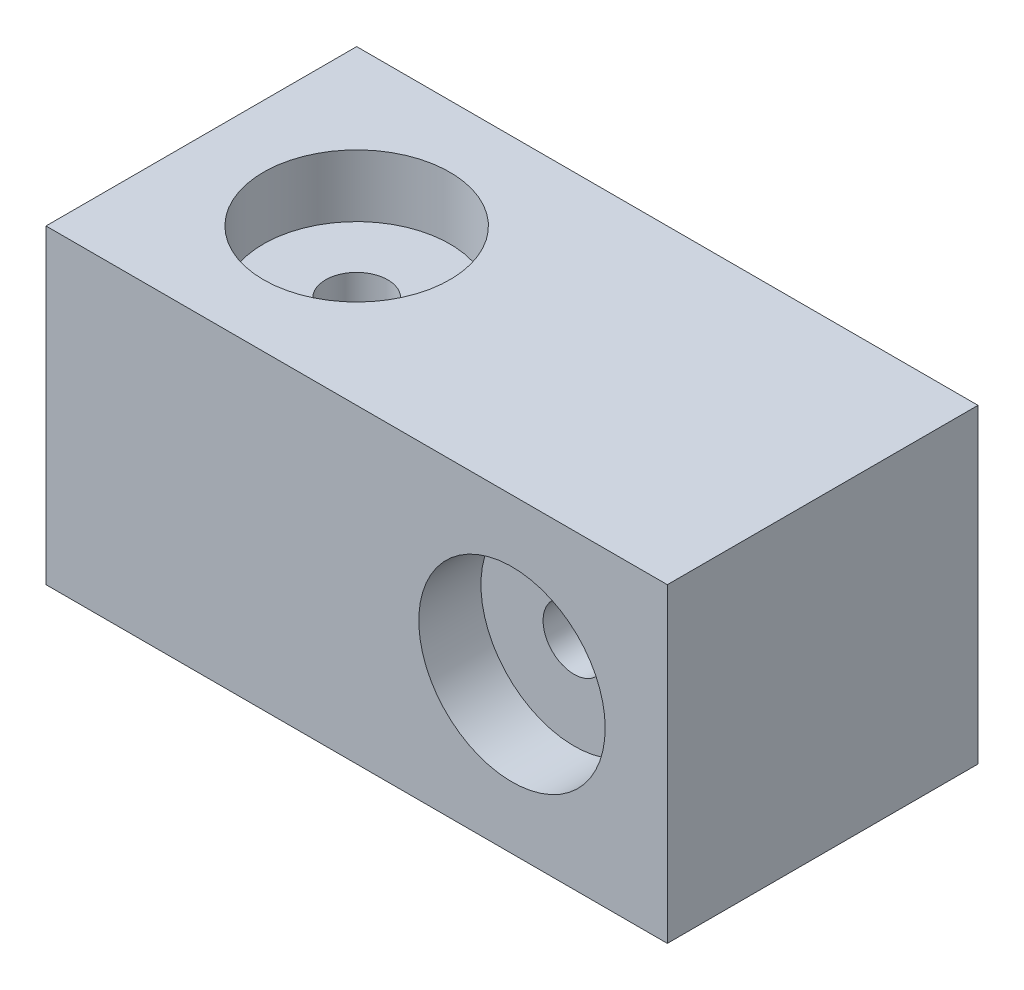
SolidWorks part; units mm, degrees
ref_plane "Front Plane" through (0, 0, 0) normal (0, 0, 1) x (1, 0, 0)
ref_plane "Top Plane" through (0, 0, 0) normal (0, 1, 0) x (1, 0, 0)
ref_plane "Right Plane" through (0, 0, 0) normal (1, 0, 0) x (0, 0, -1)
sketch "Sketch1" plane through (0, 0, 0) normal (0, 0, 1) x (1, 0, 0)
  line L1 (-24.9573, 10) -> (15.0427, 10)
  line L2 (-24.9573, 10) -> (-24.9573, -10)
  line L3 (-24.9573, -10) -> (15.0427, -10)
  line L4 (15.0427, 10) -> (15.0427, -10)
  dimension "D1" = 20
  dimension "D2" = 40
extrude "Box" add sketch "Sketch1" along normal blind 20
sketch "Sketch10" plane through (0, 0, 20) normal (0, 0, 1) x (1, 0, 0)
  line L0 (-4.9573, 10) -> (-4.9573, -10)
  line L1 (15.0427, 10) -> (-24.9573, 10) construction
  line L2 (-24.9573, -10) -> (15.0427, -10) construction
  line L3 (-4.9573, 0) -> (15.0427, 0)
  line L4 (15.0427, -10) -> (15.0427, 10) construction
  circle A0 centre (5.0427, 0) radius 6
  dimension "D1" = 12
extrude "Side Cut" cut sketch "Sketch10" against normal blind 4
sketch "Sketch11" plane through (0, 0, 20) normal (0, 0, 1) x (1, 0, 0)
  line L0 (5.0427, 6) -> (5.0427, -6)
  circle A0 centre (5.0427, 0) radius 6 construction
  circle A1 centre (5.0427, 0) radius 6 construction
  circle A2 centre (5.0427, 0) radius 2
  dimension "D1" = 4
extrude "Cut-Extrude10" cut sketch "Sketch11" against normal blind 20 contours L0 A2 | L0 A2
sketch "Sketch12" plane through (0, 10, 0) normal (0, 1, 0) x (1, 0, 0)
  line L0 (-4.9573, 0) -> (-4.9573, -20)
  line L1 (15.0427, 0) -> (-24.9573, 0) construction
  line L2 (15.0427, -20) -> (-24.9573, -20) construction
  line L3 (-24.9573, -10) -> (-4.9573, -10)
  line L4 (-24.9573, -20) -> (-24.9573, 0) construction
  circle A0 centre (-14.9573, -10) radius 6
  dimension "D1" = 12
extrude "Cut-Extrude11" cut sketch "Sketch12" against normal blind 4 contours L3 A0 | L3 A0
sketch "Sketch13" plane through (0, 10, 0) normal (0, 1, 0) x (1, 0, 0)
  line L0 (-14.9573, -4) -> (-14.9573, -16)
  circle A0 centre (-14.9573, -10) radius 6 construction
  circle A1 centre (-14.9573, -10) radius 6 construction
  circle A2 centre (-14.9573, -10) radius 2
  dimension "D1" = 4
extrude "Cut-Extrude12" cut sketch "Sketch13" against normal blind 20 contours L0 A2 | L0 A2
